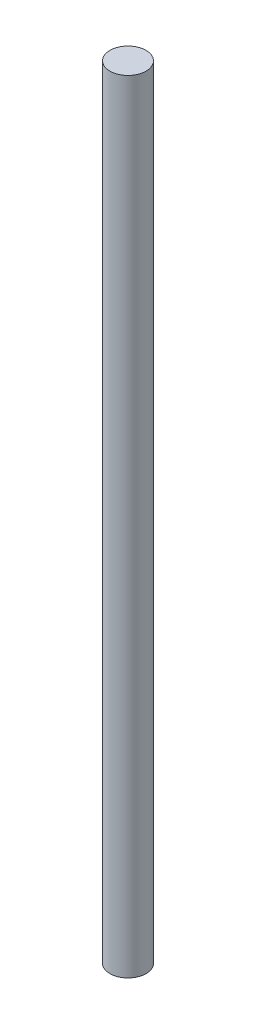
SolidWorks part; units mm, degrees
material "Plain Carbon Steel"
ref_plane "Front Plane" through (0, 0, 0) normal (0, 0, 1) x (1, 0, 0)
ref_plane "Top Plane" through (0, 0, 0) normal (0, 1, 0) x (1, 0, 0)
ref_plane "Right Plane" through (0, 0, 0) normal (1, 0, 0) x (0, 0, -1)
sketch "Sketch1" plane through (0, 0, 0) normal (0, 1, 0) x (1, 0, 0)
  circle A0 centre (0, 0) radius 1.5
  dimension "D1" = 3
extrude "Boss-Extrude1" add sketch "Sketch1" along normal blind 65
